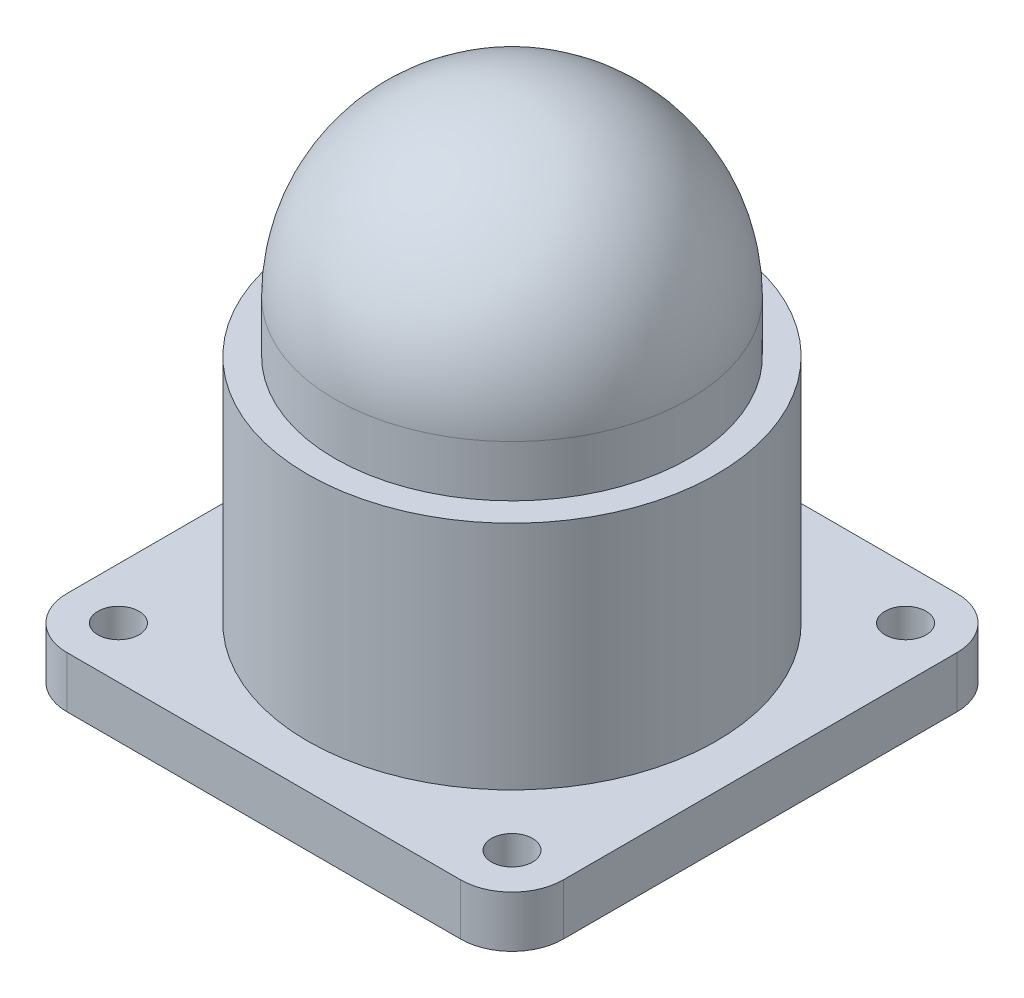
SolidWorks part; units mm, degrees
ref_plane "Front Plane" through (0, 0, 0) normal (0, 0, 1) x (1, 0, 0)
ref_plane "Top Plane" through (0, 0, 0) normal (0, 1, 0) x (1, 0, 0)
ref_plane "Right Plane" through (0, 0, 0) normal (1, 0, 0) x (0, 0, -1)
sketch "Sketch1" plane through (0, 0, 0) normal (0, 1, 0) x (1, 0, 0)
  line L0 (14.5, 29) -> (14.5, 0) construction
  line L1 (0, 0) -> (29, 0)
  line L2 (0, 0) -> (0, 29)
  line L3 (0, 29) -> (29, 29)
  line L4 (29, 0) -> (29, 29)
  line L5 (0, 14.5) -> (29, 14.5) construction
  circle A0 centre (3, 26) radius 1.2
  circle A1 centre (26, 26) radius 1.2
  circle A2 centre (26, 3) radius 1.2
  circle A3 centre (3, 3) radius 1.2
  point P10 (29, 14.5)
  dimension "D3" = 2.4
  dimension "D1" = 29
  dimension "D2" = 29
  dimension "D4" = 11.5
  dimension "D5" = 11.5
extrude "Boss-Extrude1" add sketch "Sketch1" along normal blind 3
fillet "Fillet1" radius 3 4 edges at (0, 1.5, -29) (29, 1.5, -29) (29, 1.5, 0) (0, 1.5, 0)
sketch "Sketch2" plane through (0, 3, 0) normal (0, 1, 0) x (1, 0, 0)
  line L0 (14.5, 29) -> (14.5, 0) construction
  line L1 (26, 29) -> (3, 29) construction
  line L2 (3, 0) -> (26, 0) construction
  circle A0 centre (14.5, 14.5) radius 11.95
  dimension "D1" = 23.9
extrude "Boss-Extrude2" add sketch "Sketch2" along normal blind 13.5 contours A0
sketch "Sketch3" plane through (0, 16.5, 0) normal (0, 1, 0) x (1, 0, 0)
  line L0 (14.5, 26.45) -> (14.5, 2.55) construction
  circle A0 centre (14.5, 14.5) radius 11.95 construction
  circle A1 centre (14.5, 14.5) radius 11.95 construction
  circle A2 centre (14.5, 14.5) radius 10.35
  dimension "D1" = 20.7
extrude "Boss-Extrude3" add sketch "Sketch3" along normal blind 3
ref_plane "Plane1" through (0, 0, -14.5) normal (0, 0, 1) x (1, 0, 0)
sketch "Sketch4" plane through (0, 0, -14.5) normal (0, 0, 1) x (1, 0, 0)
  line L0 (14.5, 19.5) -> (14.5, 29.85)
  line L1 (24.85, 19.5) -> (4.15, 19.5) construction
  line L2 (14.5, 19.5) -> (24.85, 19.5)
  arc A0 (24.85, 19.5) -> (14.5, 29.85) centre (14.5, 19.5) ccw
  dimension "D1" = 10.35
  dimension "D2" = 10.35
revolve "Revolve1" add sketch "Sketch4" angle 360 about L0
equation "\"D2@Sketch1\"=\"D1@Sketch1\""
equation "\"D2@Sketch4\"=\"D1@Sketch4\""
